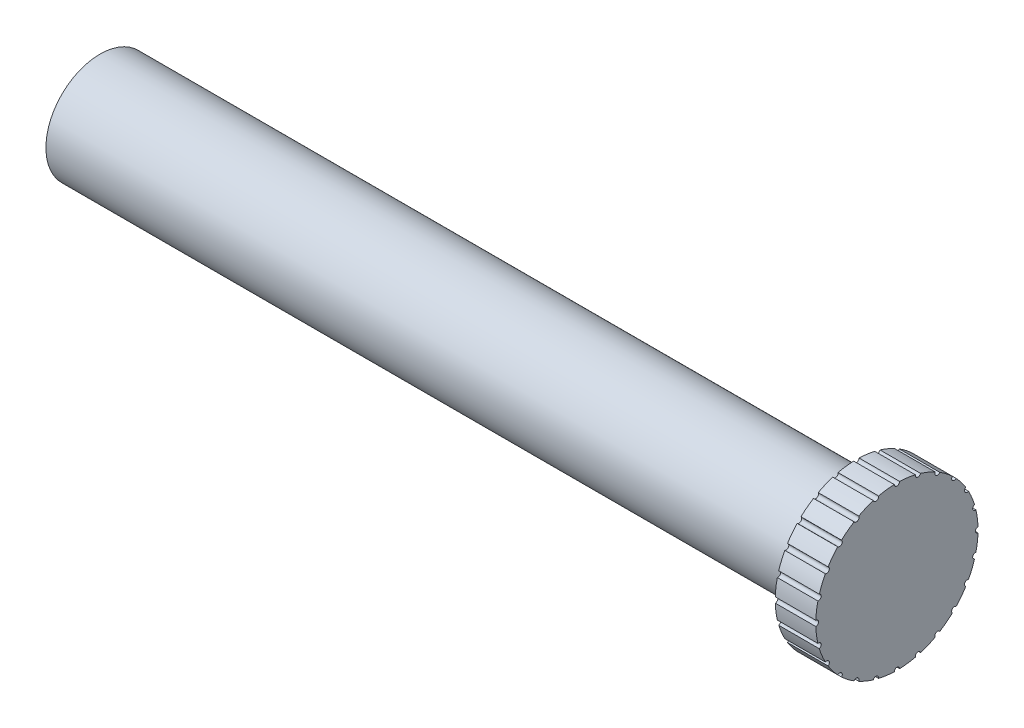
SolidWorks part; units mm, degrees
material "1060 Alloy"
ref_plane "Front Plane" through (0, 0, 0) normal (0, 0, 1) x (1, 0, 0)
ref_plane "Top Plane" through (0, 0, 0) normal (0, 1, 0) x (1, 0, 0)
ref_plane "Right Plane" through (0, 0, 0) normal (1, 0, 0) x (0, 0, -1)
sketch "Sketch1" plane through (0, 0, 0) normal (1, 0, 0) x (0, 0, -1)
  circle A0 centre (0, 0) radius 4
  dimension "D1" = 8
extrude "Boss-Extrude2" add sketch "Sketch1" along normal blind 55.94
sketch "Sketch2" plane through (55.94, 0, 0) normal (1, 0, 0) x (0, 0, -1)
  circle A0 centre (0, 0) radius 6
  dimension "D1" = 12
extrude "Boss-Extrude3" add sketch "Sketch2" along normal blind 3
sketch "Sketch3" plane through (58.94, 0, 0) normal (1, 0, 0) x (0, 0, -1)
  line L0 (-8.3009, 0) -> (10.599, 0) construction
  circle A0 centre (-6, 0) radius 0.2
  circle A1 centre (0, 0) radius 6 construction
  dimension "D1" = 0.4
extrude "Cut-Extrude1" cut sketch "Sketch3" against normal up to surface (3 mm away) up to face at (55.94, 0, -4)
pattern_circular "CirPattern1" count 25 every 15 about axis through (0, 0, -0.0033) along (1, 0, 0) of "Cut-Extrude1"
